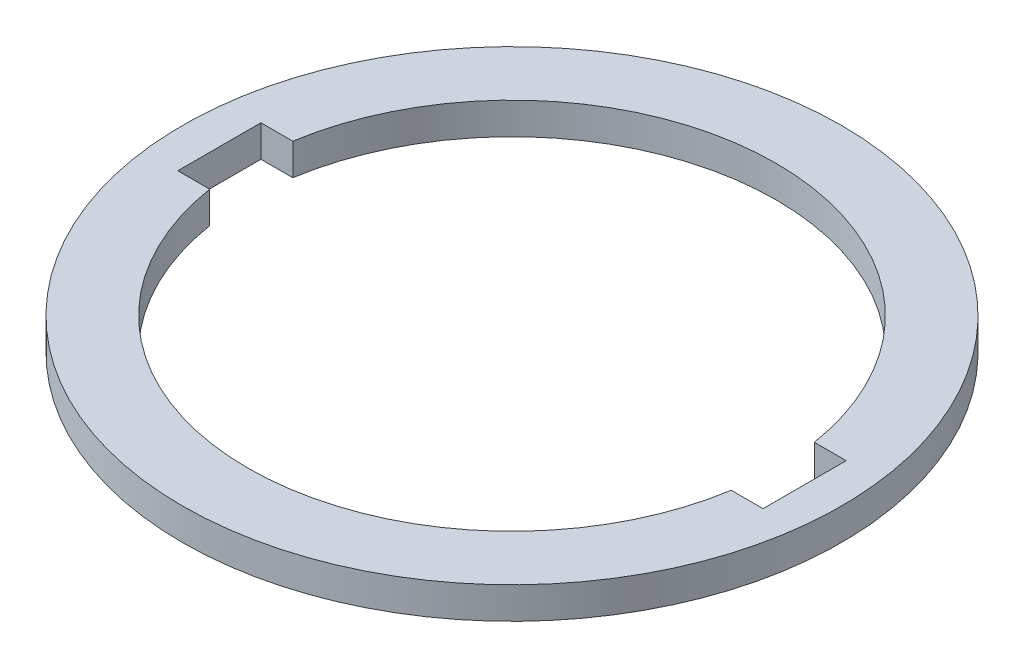
SolidWorks part; units mm, degrees
ref_plane "Front Plane" through (0, 0, 0) normal (0, 0, 1) x (1, 0, 0)
ref_plane "Top Plane" through (0, 0, 0) normal (0, 1, 0) x (1, 0, 0)
ref_plane "Right Plane" through (0, 0, 0) normal (1, 0, 0) x (0, 0, -1)
sketch "Sketch2" plane through (0, 0, 0) normal (0, 1, 0) x (1, 0, 0)
  circle A0 centre (0, 0) radius 49.55
  circle A1 centre (0, 0) radius 39.7
  dimension "D1" = 99.1
  dimension "D2" = 79.4
extrude "Boss-Extrude1" add sketch "Sketch2" along normal blind 4.7625
sketch "Sketch3" plane through (0, 4.7625, 0) normal (0, 1, 0) x (1, 0, 0)
  line L1 (-44, -6.25) -> (44, -6.25)
  line L2 (-44, -6.25) -> (-44, 6.25)
  line L3 (-44, 6.25) -> (44, 6.25)
  line L4 (44, -6.25) -> (44, 6.25)
  line L5 (-44, -6.25) -> (44, 6.25) construction
  line L6 (-44, 6.25) -> (44, -6.25) construction
  point P0 (0, 0)
  dimension "D1" = 88
  dimension "D2" = 12.5
extrude "Cut-Extrude1" cut sketch "Sketch3" against normal through all
